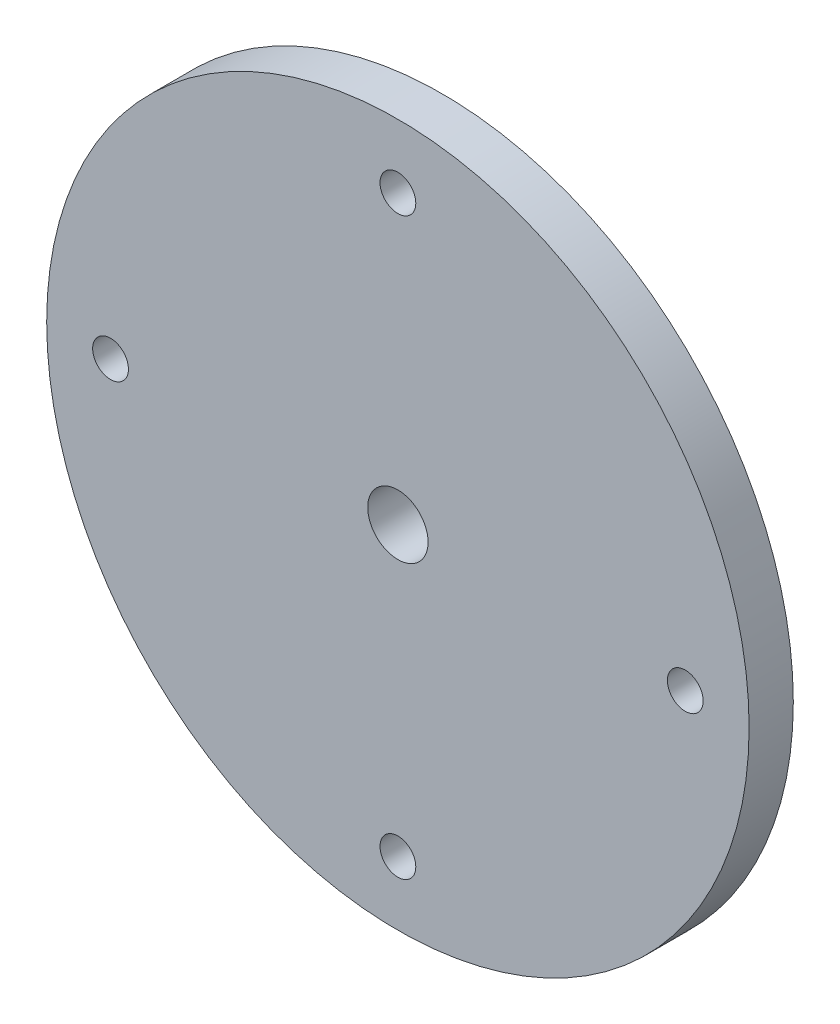
SolidWorks part; units mm, degrees
ref_plane "Front Plane" through (0, 0, 0) normal (0, 0, 1) x (1, 0, 0)
ref_plane "Top Plane" through (0, 0, 0) normal (0, 1, 0) x (1, 0, 0)
ref_plane "Right Plane" through (0, 0, 0) normal (1, 0, 0) x (0, 0, -1)
sketch "Sketch1" plane through (0, 0, 0) normal (0, 0, 1) x (1, 0, 0)
  line L0 (0, 28.575) -> (0, 0) construction
  circle A0 centre (0, 0) radius 34.925
  circle A1 centre (0, 0) radius 3
  circle A2 centre (0, 28.575) radius 1.778
  circle A3 centre (28.575, 0) radius 1.778
  circle A4 centre (0, -28.575) radius 1.778
  circle A5 centre (-28.575, 0) radius 1.778
  point P15 (0, 0)
  dimension "D1" = 69.85
  dimension "D2" = 6
  dimension "D3" = 3.556
  dimension "D5" = 28.575
  dimension "D4" = 4
extrude "Boss-Extrude1" add sketch "Sketch1" along normal blind 4.3942
